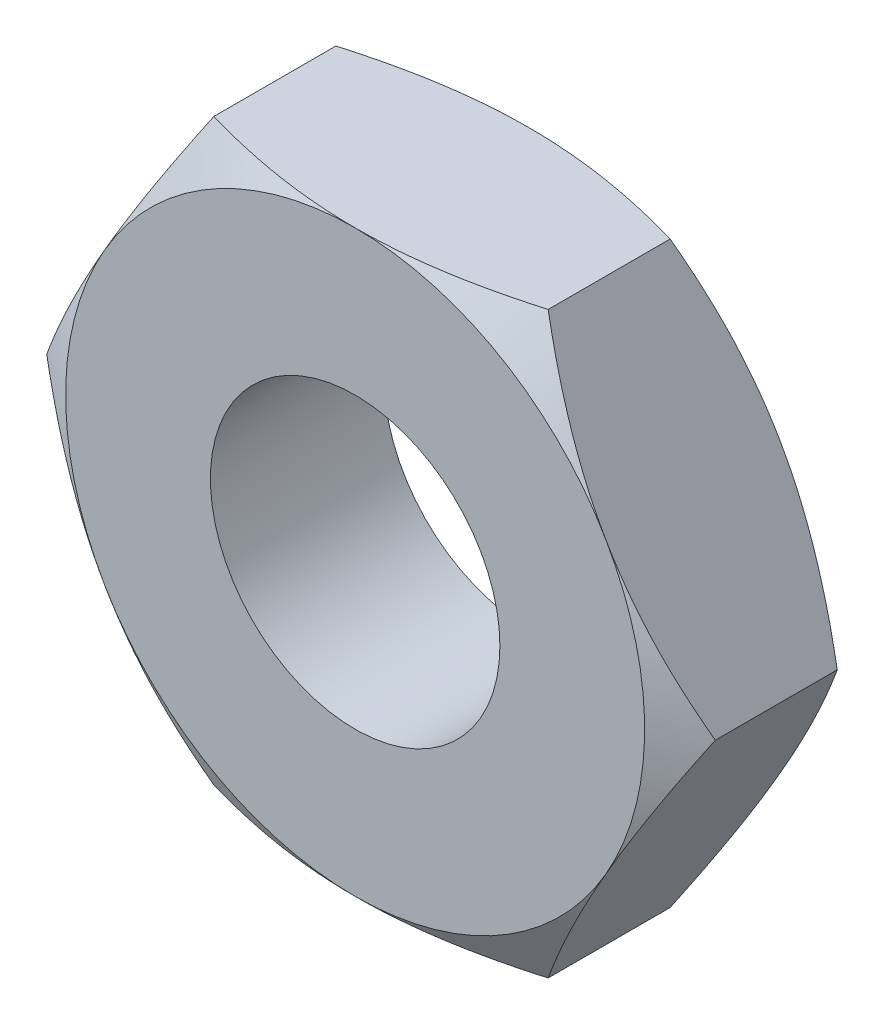
SolidWorks part; units mm, degrees
material "AISI 316 (A4) Annealed Stainless Bar"
ref_plane "Front" through (0, 0, 0) normal (0, 0, 1) x (1, 0, 0)
ref_plane "Top" through (0, 0, 0) normal (0, 1, 0) x (1, 0, 0)
ref_plane "Right" through (0, 0, 0) normal (1, 0, 0) x (0, 0, -1)
sketch "HexSketch1" plane through (0, 0, 0) normal (0, 0, 1) x (1, 0, 0)
  line L1 (1.1547, 2) -> (-1.1547, 2)
  line L2 (-1.1547, 2) -> (-2.3094, 0)
  line L3 (-2.3094, 0) -> (-1.1547, -2)
  line L4 (-1.1547, -2) -> (1.1547, -2)
  line L5 (1.1547, -2) -> (2.3094, 0)
  line L6 (2.3094, 0) -> (1.1547, 2)
  circle A0 centre (0, 0) radius 2 construction
extrude "Hex" add sketch "HexSketch1" against normal blind 1.2
ref_plane "Nut_Top_Plane" through (0, 0, 0) normal (0, 0, 1) x (1, 0, 0)
ref_plane "Collar_Top_Plane" through (0, 0, 4.8) normal (0, 0, -1) x (-1, 0, 0)
sketch "Lock Collar BossSketch2" plane through (0, 0, 0) normal (0, 0, 1) x (1, 0, 0)
  circle A0 centre (0, 0) radius 2
sketch "Plastic_SleeveSketch5" plane through (0, 0, 4.8) normal (0, 0, -1) x (-1, 0, 0)
  circle A0 centre (0, 0) radius 1
  circle A1 centre (0, 0) radius 4
  dimension "INSERT_OD" = 8
ref_axis "Axis1" through (0, 0, 50) along (0, 0, -1)
sketch "Thread_BoreSketch4" plane through (0, 0, 0) normal (0, 0, 1) x (1, 0, 0)
  circle A0 centre (0, 0) radius 1
extrude "Thread_Bore" cut sketch "Thread_BoreSketch4" against normal through all
ref_plane "CORNERSPlane3" through (0, 0, 0) normal (0.866, 0.5, 0) x (0, 0, -1)
sketch "NUT_CHAMFERSketch10" plane through (0, 0, 0) normal (0.866, 0.5, 0) x (0, 0, -1)
  line L0 (0, 2) -> (0.1786, 2.3094)
  line L1 (1.2, 2.3094) -> (0, 2.3094) construction
  line L2 (0.1786, 2.3094) -> (0, 2.3094)
  line L3 (0, 2.3094) -> (0, 2)
  line L4 (0.6, 2.3094) -> (0.6, -2.3094) construction
  line L5 (1.2, -2.3094) -> (0, -2.3094) construction
  line L6 (1.2, 2) -> (1.0214, 2.3094)
  line L7 (1.0214, 2.3094) -> (1.2, 2.3094)
  line L8 (1.2, 2.3094) -> (1.2, 2)
  dimension "D1" = 30
  dimension "D2" = 2
revolve "NUT_CHAMFER" cut sketch "NUT_CHAMFERSketch10" angle 360 about axis through (0, 0, 50) along (0, 0, -1)
equation "\"D2@NUT_CHAMFERSketch10\" = \"A/F\"/2"
